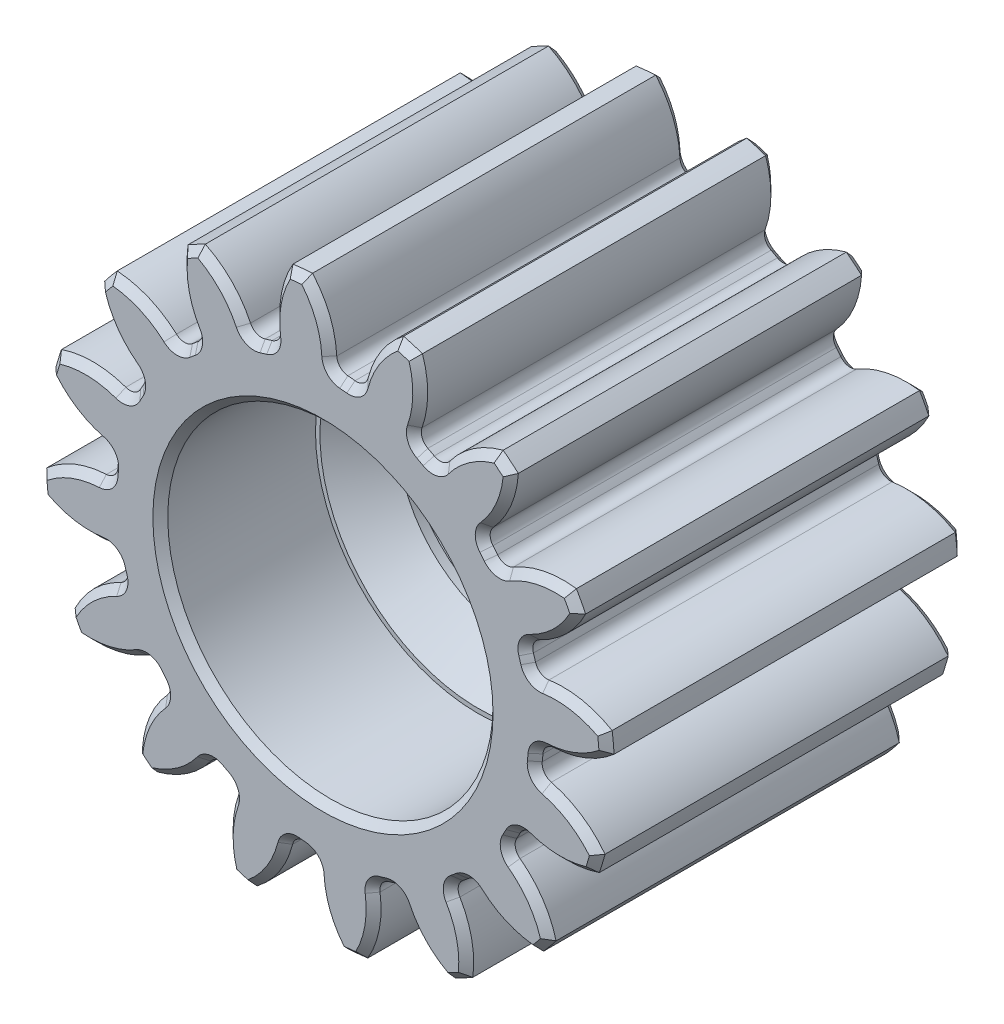
SolidWorks part; units mm, degrees
ref_plane "Front" through (0, 0, 0) normal (0, 0, 1) x (1, 0, 0)
ref_plane "Top" through (0, 0, 0) normal (0, 1, 0) x (1, 0, 0)
ref_plane "Right" through (0, 0, 0) normal (1, 0, 0) x (0, 0, -1)
sketch "Sketch3" plane through (0, 0, 0) normal (0, 0, 1) x (1, 0, 0)
  circle A0 centre (0, 0) radius 9.525
  dimension "od" = 19.05
extrude "gearBody" add sketch "Sketch3" along normal blind 12
sketch "Sketch2" plane through (0, 0, 0) normal (0, 0, 1) x (1, 0, 0)
  line L0 (0, 0) -> (7.3504, 3.0447) construction
  line L1 (9.6113, -3.1572) -> (0, 0) construction
  line L2 (0, 0) -> (36.3143, 0) construction
  line L3 (8.4666, -0.0191) -> (8.3054, -1.6447) construction
  line L5 (8.386, -0.8319) -> (0, 0) construction
  line L7 (0, 0) -> (7.9561, 0) construction
  arc A0 (7.9545, -0.1597) -> (7.8308, -1.4063) centre (0, 0) ccw construction
  arc A1 (9.5062, 0.5982) -> (9.2034, -2.4542) centre (0, 0) ccw construction
  arc A2 (8.4666, -0.0191) -> (8.3054, -1.6447) centre (0, 0) ccw construction
  arc A3 (7.098, -0.8257) -> (7.1219, -0.585) centre (0, 0) ccw
  arc A4 (9.6113, -3.1572) -> (7.4028, -1.2668) centre (6.609, -4.4295) ccw
  arc A5 (9.6113, -3.1572) -> (10.0443, 1.2073) centre (0, 0) ccw
  arc A6 (10.0443, 1.2073) -> (7.5074, -0.2123) centre (7.3504, 3.0447) cw
  arc A7 (7.1219, -0.585) -> (7.5074, -0.2123) centre (7.5269, -0.6183) cw
  arc A8 (7.4028, -1.2668) -> (7.098, -0.8257) centre (7.5017, -0.8726) cw
  point P6 (10.0443, 1.2073)
  point P22 (9.6113, -3.1572)
  dimension "baseDia" = 15.9121
  dimension "od" = 19.05
  dimension "pd" = 16.9333
  dimension "rd" = 14.2917
  dimension "rFillet" = 0.4064
  dimension "pointX" = 10.0443
  dimension "pointY" = 1.2073
  dimension "CTT" = 1.6256
  dimension "flankCenterAngle" = 22.5
extrude "toothCut" cut sketch "Sketch2" along normal through all
pattern_circular "CirPattern1" count 16 over 360 about axis through (0, 0, 0) along (0, 0, 1) of "toothCut"
sketch "hub1Dia" plane through (0, 0, 0) normal (0, 0, -1) x (-1, 0, 0)
  circle A0 centre (0, 0) radius 12.7
  dimension "hub1Dia" = 25.4
sketch "hub2Dia" plane through (0, 0, 12) normal (0, 0, 1) x (1, 0, 0)
  circle A0 centre (0, 0) radius 12.7
  dimension "hub2dia" = 25.4
sketch "boreDia" plane through (0, 0, 0) normal (0, 0, 1) x (1, 0, 0)
  circle A0 centre (0, 0) radius 4
  dimension "boreDia" = 8
extrude "bore" cut sketch "boreDia" against normal mid plane 25400
sketch "Sketch5" plane through (0, 0, 0) normal (0, 0, -1) x (-1, 0, 0)
  circle A0 centre (0, 0) radius 5.45
  dimension "D1" = 10.9
extrude "Cut-Extrude2" cut sketch "Sketch5" against normal blind 5.2
sketch "Sketch6" plane through (0, 0, 12) normal (0, 0, 1) x (1, 0, 0)
  circle A0 centre (0, 0) radius 5.45
  dimension "D1" = 10.9
extrude "Cut-Extrude3" cut sketch "Sketch6" against normal blind 5.2
sketch "Sketch7" plane through (0, 0, 12) normal (0, 0, 1) x (1, 0, 0)
  circle A96 centre (0, 0) radius 6.178
  arc A192 (7.1876, -6.4015) -> (7.6725, -5.8115) centre (0, 0) ccw
  arc A193 (7.6725, -5.8115) -> (6.4141, -3.923) centre (4.4108, -6.6214) ccw
  arc A194 (6.3291, -3.5278) -> (6.4141, -3.923) centre (6.5967, -3.677) ccw
  arc A195 (6.3291, -3.5278) -> (6.4448, -3.3116) centre (0, 0) ccw
  arc A196 (6.8209, -3.1632) -> (6.4448, -3.3116) centre (6.7174, -3.4516) ccw
  arc A197 (6.8209, -3.1632) -> (9.0902, -3.1636) centre (7.9561, 0) ccw
  arc A198 (9.0902, -3.1636) -> (9.3124, -2.4329) centre (0, 0) ccw
  arc A199 (9.3124, -2.4329) -> (7.4271, -1.1698) centre (6.609, -4.4295) ccw
  arc A200 (7.1973, -0.8372) -> (7.4271, -1.1698) centre (7.5017, -0.8726) ccw
  arc A201 (7.1973, -0.8372) -> (7.2215, -0.5932) centre (0, 0) ccw
  arc A202 (7.5122, -0.3122) -> (7.2215, -0.5932) centre (7.5269, -0.6183) ccw
  arc A203 (7.5122, -0.3122) -> (9.6089, 0.5559) centre (7.3504, 3.0447) ccw
  arc A204 (9.6089, 0.5559) -> (9.5346, 1.316) centre (0, 0) ccw
  arc A205 (9.5346, 1.316) -> (7.3094, 1.7615) centre (7.801, -1.5631) ccw
  arc A206 (6.9699, 1.9808) -> (7.3094, 1.7615) centre (7.2646, 2.0646) ccw
  arc A207 (6.9699, 1.9808) -> (6.8988, 2.2155) centre (0, 0) ccw
  arc A208 (7.0598, 2.5863) -> (6.8988, 2.2155) centre (7.1906, 2.3092) ccw
  arc A209 (7.0598, 2.5863) -> (8.6648, 4.1908) centre (5.6258, 5.6258) ccw
  arc A210 (8.6648, 4.1908) -> (8.3052, 4.8645) centre (0, 0) ccw
  arc A211 (8.3052, 4.8645) -> (6.0789, 4.4246) centre (7.8054, 1.5412) ccw
  arc A212 (5.6813, 4.4973) -> (6.0789, 4.4246) centre (5.9215, 4.6875) ccw
  arc A213 (5.6813, 4.4973) -> (5.5258, 4.687) centre (0, 0) ccw
  arc A214 (5.5327, 5.0911) -> (5.5258, 4.687) centre (5.7595, 4.8852) ccw
  arc A215 (5.5327, 5.0911) -> (6.4015, 7.1876) centre (3.0447, 7.3504) ccw
  arc A216 (6.4015, 7.1876) -> (5.8115, 7.6725) centre (0, 0) ccw
  arc A217 (5.8115, 7.6725) -> (3.923, 6.4141) centre (6.6214, 4.4108) ccw
  arc A218 (3.5278, 6.3291) -> (3.923, 6.4141) centre (3.677, 6.5967) ccw
  arc A219 (3.5278, 6.3291) -> (3.3116, 6.4448) centre (0, 0) ccw
  arc A220 (3.1632, 6.8209) -> (3.3116, 6.4448) centre (3.4516, 6.7174) ccw
  arc A221 (3.1632, 6.8209) -> (3.1636, 9.0902) centre (0, 7.9561) ccw
  arc A222 (3.1636, 9.0902) -> (2.4329, 9.3124) centre (0, 0) ccw
  arc A223 (2.4329, 9.3124) -> (1.1698, 7.4271) centre (4.4295, 6.609) ccw
  arc A224 (0.8372, 7.1973) -> (1.1698, 7.4271) centre (0.8726, 7.5017) ccw
  arc A225 (0.8372, 7.1973) -> (0.5932, 7.2215) centre (0, 0) ccw
  arc A226 (0.3122, 7.5122) -> (0.5932, 7.2215) centre (0.6183, 7.5269) ccw
  arc A227 (0.3122, 7.5122) -> (-0.5559, 9.6089) centre (-3.0447, 7.3504) ccw
  arc A228 (-0.5559, 9.6089) -> (-1.316, 9.5346) centre (0, 0) ccw
  arc A229 (-1.316, 9.5346) -> (-1.7615, 7.3094) centre (1.5631, 7.801) ccw
  arc A230 (-1.9808, 6.9699) -> (-1.7615, 7.3094) centre (-2.0646, 7.2646) ccw
  arc A231 (-1.9808, 6.9699) -> (-2.2155, 6.8988) centre (0, 0) ccw
  arc A232 (-2.5863, 7.0598) -> (-2.2155, 6.8988) centre (-2.3092, 7.1906) ccw
  arc A233 (-2.5863, 7.0598) -> (-4.1908, 8.6648) centre (-5.6258, 5.6258) ccw
  arc A234 (-4.1908, 8.6648) -> (-4.8645, 8.3052) centre (0, 0) ccw
  arc A235 (-4.8645, 8.3052) -> (-4.4246, 6.0789) centre (-1.5412, 7.8054) ccw
  arc A236 (-4.4973, 5.6813) -> (-4.4246, 6.0789) centre (-4.6875, 5.9215) ccw
  arc A237 (-4.4973, 5.6813) -> (-4.687, 5.5258) centre (0, 0) ccw
  arc A238 (-5.0911, 5.5327) -> (-4.687, 5.5258) centre (-4.8852, 5.7595) ccw
  arc A239 (-5.0911, 5.5327) -> (-7.1876, 6.4015) centre (-7.3504, 3.0447) ccw
  arc A240 (-7.1876, 6.4015) -> (-7.6725, 5.8115) centre (0, 0) ccw
  arc A241 (-7.6725, 5.8115) -> (-6.4141, 3.923) centre (-4.4108, 6.6214) ccw
  arc A242 (-6.3291, 3.5278) -> (-6.4141, 3.923) centre (-6.5967, 3.677) ccw
  arc A243 (-6.3291, 3.5278) -> (-6.4448, 3.3116) centre (0, 0) ccw
  arc A244 (-6.8209, 3.1632) -> (-6.4448, 3.3116) centre (-6.7174, 3.4516) ccw
  arc A245 (-6.8209, 3.1632) -> (-9.0902, 3.1636) centre (-7.9561, 0) ccw
  arc A246 (-9.0902, 3.1636) -> (-9.3124, 2.4329) centre (0, 0) ccw
  arc A247 (-9.3124, 2.4329) -> (-7.4271, 1.1698) centre (-6.609, 4.4295) ccw
  arc A248 (-7.1973, 0.8372) -> (-7.4271, 1.1698) centre (-7.5017, 0.8726) ccw
  arc A249 (-7.1973, 0.8372) -> (-7.2215, 0.5932) centre (0, 0) ccw
  arc A250 (-7.5122, 0.3122) -> (-7.2215, 0.5932) centre (-7.5269, 0.6183) ccw
  arc A251 (-7.5122, 0.3122) -> (-9.6089, -0.5559) centre (-7.3504, -3.0447) ccw
  arc A252 (-9.6089, -0.5559) -> (-9.5346, -1.316) centre (0, 0) ccw
  arc A253 (-9.5346, -1.316) -> (-7.3094, -1.7615) centre (-7.801, 1.5631) ccw
  arc A254 (-6.9699, -1.9808) -> (-7.3094, -1.7615) centre (-7.2646, -2.0646) ccw
  arc A255 (-6.9699, -1.9808) -> (-6.8988, -2.2155) centre (0, 0) ccw
  arc A256 (-7.0598, -2.5863) -> (-6.8988, -2.2155) centre (-7.1906, -2.3092) ccw
  arc A257 (-7.0598, -2.5863) -> (-8.6648, -4.1908) centre (-5.6258, -5.6258) ccw
  arc A258 (-8.6648, -4.1908) -> (-8.3052, -4.8645) centre (0, 0) ccw
  arc A259 (-8.3052, -4.8645) -> (-6.0789, -4.4246) centre (-7.8054, -1.5412) ccw
  arc A260 (-5.6813, -4.4973) -> (-6.0789, -4.4246) centre (-5.9215, -4.6875) ccw
  arc A261 (-5.6813, -4.4973) -> (-5.5258, -4.687) centre (0, 0) ccw
  arc A262 (-5.5327, -5.0911) -> (-5.5258, -4.687) centre (-5.7595, -4.8852) ccw
  arc A263 (-5.5327, -5.0911) -> (-6.4015, -7.1876) centre (-3.0447, -7.3504) ccw
  arc A264 (-6.4015, -7.1876) -> (-5.8115, -7.6725) centre (0, 0) ccw
  arc A265 (-5.8115, -7.6725) -> (-3.923, -6.4141) centre (-6.6214, -4.4108) ccw
  arc A266 (-3.5278, -6.3291) -> (-3.923, -6.4141) centre (-3.677, -6.5967) ccw
  arc A267 (-3.5278, -6.3291) -> (-3.3116, -6.4448) centre (0, 0) ccw
  arc A268 (-3.1632, -6.8209) -> (-3.3116, -6.4448) centre (-3.4516, -6.7174) ccw
  arc A269 (-3.1632, -6.8209) -> (-3.1636, -9.0902) centre (0, -7.9561) ccw
  arc A270 (-3.1636, -9.0902) -> (-2.4329, -9.3124) centre (0, 0) ccw
  arc A271 (-2.4329, -9.3124) -> (-1.1698, -7.4271) centre (-4.4295, -6.609) ccw
  arc A272 (-0.8372, -7.1973) -> (-1.1698, -7.4271) centre (-0.8726, -7.5017) ccw
  arc A273 (-0.8372, -7.1973) -> (-0.5932, -7.2215) centre (0, 0) ccw
  arc A274 (-0.3122, -7.5122) -> (-0.5932, -7.2215) centre (-0.6183, -7.5269) ccw
  arc A275 (-0.3122, -7.5122) -> (0.5559, -9.6089) centre (3.0447, -7.3504) ccw
  arc A276 (0.5559, -9.6089) -> (1.316, -9.5346) centre (0, 0) ccw
  arc A277 (1.316, -9.5346) -> (1.7615, -7.3094) centre (-1.5631, -7.801) ccw
  arc A278 (1.9808, -6.9699) -> (1.7615, -7.3094) centre (2.0646, -7.2646) ccw
  arc A279 (1.9808, -6.9699) -> (2.2155, -6.8988) centre (0, 0) ccw
  arc A280 (2.5863, -7.0598) -> (2.2155, -6.8988) centre (2.3092, -7.1906) ccw
  arc A281 (2.5863, -7.0598) -> (4.1908, -8.6648) centre (5.6258, -5.6258) ccw
  arc A282 (4.1908, -8.6648) -> (4.8645, -8.3052) centre (0, 0) ccw
  arc A283 (4.8645, -8.3052) -> (4.4246, -6.0789) centre (1.5412, -7.8054) ccw
  arc A284 (4.4973, -5.6813) -> (4.4246, -6.0789) centre (4.6875, -5.9215) ccw
  arc A285 (4.4973, -5.6813) -> (4.687, -5.5258) centre (0, 0) ccw
  arc A286 (5.0911, -5.5327) -> (4.687, -5.5258) centre (4.8852, -5.7595) ccw
  arc A287 (5.0911, -5.5327) -> (7.1876, -6.4015) centre (7.3504, -3.0447) ccw
  arc A288 (7.1876, -6.4015) -> (7.6725, -5.8115) centre (0, 0) ccw
  arc A289 (7.6725, -5.8115) -> (6.4141, -3.923) centre (4.4108, -6.6214) ccw
  arc A290 (6.3291, -3.5278) -> (6.4141, -3.923) centre (6.5967, -3.677) ccw
  arc A291 (6.3291, -3.5278) -> (6.4448, -3.3116) centre (0, 0) ccw
  arc A292 (6.8209, -3.1632) -> (6.4448, -3.3116) centre (6.7174, -3.4516) ccw
  arc A293 (6.8209, -3.1632) -> (9.0902, -3.1636) centre (7.9561, 0) ccw
  arc A294 (9.0902, -3.1636) -> (9.3124, -2.4329) centre (0, 0) ccw
  arc A295 (9.3124, -2.4329) -> (7.4271, -1.1698) centre (6.609, -4.4295) ccw
  arc A296 (7.1973, -0.8372) -> (7.4271, -1.1698) centre (7.5017, -0.8726) ccw
  arc A297 (7.1973, -0.8372) -> (7.2215, -0.5932) centre (0, 0) ccw
  arc A298 (7.5122, -0.3122) -> (7.2215, -0.5932) centre (7.5269, -0.6183) ccw
  arc A299 (7.5122, -0.3122) -> (9.6089, 0.5559) centre (7.3504, 3.0447) ccw
  arc A300 (9.6089, 0.5559) -> (9.5346, 1.316) centre (0, 0) ccw
  arc A301 (9.5346, 1.316) -> (7.3094, 1.7615) centre (7.801, -1.5631) ccw
  arc A302 (6.9699, 1.9808) -> (7.3094, 1.7615) centre (7.2646, 2.0646) ccw
  arc A303 (6.9699, 1.9808) -> (6.8988, 2.2155) centre (0, 0) ccw
  arc A304 (7.0598, 2.5863) -> (6.8988, 2.2155) centre (7.1906, 2.3092) ccw
  arc A305 (7.0598, 2.5863) -> (8.6648, 4.1908) centre (5.6258, 5.6258) ccw
  arc A306 (8.6648, 4.1908) -> (8.3052, 4.8645) centre (0, 0) ccw
  arc A307 (8.3052, 4.8645) -> (6.0789, 4.4246) centre (7.8054, 1.5412) ccw
  arc A308 (5.6813, 4.4973) -> (6.0789, 4.4246) centre (5.9215, 4.6875) ccw
  arc A309 (5.6813, 4.4973) -> (5.5258, 4.687) centre (0, 0) ccw
  arc A310 (5.5327, 5.0911) -> (5.5258, 4.687) centre (5.7595, 4.8852) ccw
  arc A311 (5.5327, 5.0911) -> (6.4015, 7.1876) centre (3.0447, 7.3504) ccw
  arc A312 (6.4015, 7.1876) -> (5.8115, 7.6725) centre (0, 0) ccw
  arc A313 (5.8115, 7.6725) -> (3.923, 6.4141) centre (6.6214, 4.4108) ccw
  arc A314 (3.5278, 6.3291) -> (3.923, 6.4141) centre (3.677, 6.5967) ccw
  arc A315 (3.5278, 6.3291) -> (3.3116, 6.4448) centre (0, 0) ccw
  arc A316 (3.1632, 6.8209) -> (3.3116, 6.4448) centre (3.4516, 6.7174) ccw
  arc A317 (3.1632, 6.8209) -> (3.1636, 9.0902) centre (0, 7.9561) ccw
  arc A318 (3.1636, 9.0902) -> (2.4329, 9.3124) centre (0, 0) ccw
  arc A319 (2.4329, 9.3124) -> (1.1698, 7.4271) centre (4.4295, 6.609) ccw
  arc A320 (0.8372, 7.1973) -> (1.1698, 7.4271) centre (0.8726, 7.5017) ccw
  arc A321 (0.8372, 7.1973) -> (0.5932, 7.2215) centre (0, 0) ccw
  arc A322 (0.3122, 7.5122) -> (0.5932, 7.2215) centre (0.6183, 7.5269) ccw
  arc A323 (0.3122, 7.5122) -> (-0.5559, 9.6089) centre (-3.0447, 7.3504) ccw
  arc A324 (-0.5559, 9.6089) -> (-1.316, 9.5346) centre (0, 0) ccw
  arc A325 (-1.316, 9.5346) -> (-1.7615, 7.3094) centre (1.5631, 7.801) ccw
  arc A326 (-1.9808, 6.9699) -> (-1.7615, 7.3094) centre (-2.0646, 7.2646) ccw
  arc A327 (-1.9808, 6.9699) -> (-2.2155, 6.8988) centre (0, 0) ccw
  arc A328 (-2.5863, 7.0598) -> (-2.2155, 6.8988) centre (-2.3092, 7.1906) ccw
  arc A329 (-2.5863, 7.0598) -> (-4.1908, 8.6648) centre (-5.6258, 5.6258) ccw
  arc A330 (-4.1908, 8.6648) -> (-4.8645, 8.3052) centre (0, 0) ccw
  arc A331 (-4.8645, 8.3052) -> (-4.4246, 6.0789) centre (-1.5412, 7.8054) ccw
  arc A332 (-4.4973, 5.6813) -> (-4.4246, 6.0789) centre (-4.6875, 5.9215) ccw
  arc A333 (-4.4973, 5.6813) -> (-4.687, 5.5258) centre (0, 0) ccw
  arc A334 (-5.0911, 5.5327) -> (-4.687, 5.5258) centre (-4.8852, 5.7595) ccw
  arc A335 (-5.0911, 5.5327) -> (-7.1876, 6.4015) centre (-7.3504, 3.0447) ccw
  arc A336 (-7.1876, 6.4015) -> (-7.6725, 5.8115) centre (0, 0) ccw
  arc A337 (-7.6725, 5.8115) -> (-6.4141, 3.923) centre (-4.4108, 6.6214) ccw
  arc A338 (-6.3291, 3.5278) -> (-6.4141, 3.923) centre (-6.5967, 3.677) ccw
  arc A339 (-6.3291, 3.5278) -> (-6.4448, 3.3116) centre (0, 0) ccw
  arc A340 (-6.8209, 3.1632) -> (-6.4448, 3.3116) centre (-6.7174, 3.4516) ccw
  arc A341 (-6.8209, 3.1632) -> (-9.0902, 3.1636) centre (-7.9561, 0) ccw
  arc A342 (-9.0902, 3.1636) -> (-9.3124, 2.4329) centre (0, 0) ccw
  arc A343 (-9.3124, 2.4329) -> (-7.4271, 1.1698) centre (-6.609, 4.4295) ccw
  arc A344 (-7.1973, 0.8372) -> (-7.4271, 1.1698) centre (-7.5017, 0.8726) ccw
  arc A345 (-7.1973, 0.8372) -> (-7.2215, 0.5932) centre (0, 0) ccw
  arc A346 (-7.5122, 0.3122) -> (-7.2215, 0.5932) centre (-7.5269, 0.6183) ccw
  arc A347 (-7.5122, 0.3122) -> (-9.6089, -0.5559) centre (-7.3504, -3.0447) ccw
  arc A348 (-9.6089, -0.5559) -> (-9.5346, -1.316) centre (0, 0) ccw
  arc A349 (-9.5346, -1.316) -> (-7.3094, -1.7615) centre (-7.801, 1.5631) ccw
  arc A350 (-6.9699, -1.9808) -> (-7.3094, -1.7615) centre (-7.2646, -2.0646) ccw
  arc A351 (-6.9699, -1.9808) -> (-6.8988, -2.2155) centre (0, 0) ccw
  arc A352 (-7.0598, -2.5863) -> (-6.8988, -2.2155) centre (-7.1906, -2.3092) ccw
  arc A353 (-7.0598, -2.5863) -> (-8.6648, -4.1908) centre (-5.6258, -5.6258) ccw
  arc A354 (-8.6648, -4.1908) -> (-8.3052, -4.8645) centre (0, 0) ccw
  arc A355 (-8.3052, -4.8645) -> (-6.0789, -4.4246) centre (-7.8054, -1.5412) ccw
  arc A356 (-5.6813, -4.4973) -> (-6.0789, -4.4246) centre (-5.9215, -4.6875) ccw
  arc A357 (-5.6813, -4.4973) -> (-5.5258, -4.687) centre (0, 0) ccw
  arc A358 (-5.5327, -5.0911) -> (-5.5258, -4.687) centre (-5.7595, -4.8852) ccw
  arc A359 (-5.5327, -5.0911) -> (-6.4015, -7.1876) centre (-3.0447, -7.3504) ccw
  arc A360 (-6.4015, -7.1876) -> (-5.8115, -7.6725) centre (0, 0) ccw
  arc A361 (-5.8115, -7.6725) -> (-3.923, -6.4141) centre (-6.6214, -4.4108) ccw
  arc A362 (-3.5278, -6.3291) -> (-3.923, -6.4141) centre (-3.677, -6.5967) ccw
  arc A363 (-3.5278, -6.3291) -> (-3.3116, -6.4448) centre (0, 0) ccw
  arc A364 (-3.1632, -6.8209) -> (-3.3116, -6.4448) centre (-3.4516, -6.7174) ccw
  arc A365 (-3.1632, -6.8209) -> (-3.1636, -9.0902) centre (0, -7.9561) ccw
  arc A366 (-3.1636, -9.0902) -> (-2.4329, -9.3124) centre (0, 0) ccw
  arc A367 (-2.4329, -9.3124) -> (-1.1698, -7.4271) centre (-4.4295, -6.609) ccw
  arc A368 (-0.8372, -7.1973) -> (-1.1698, -7.4271) centre (-0.8726, -7.5017) ccw
  arc A369 (-0.8372, -7.1973) -> (-0.5932, -7.2215) centre (0, 0) ccw
  arc A370 (-0.3122, -7.5122) -> (-0.5932, -7.2215) centre (-0.6183, -7.5269) ccw
  arc A371 (-0.3122, -7.5122) -> (0.5559, -9.6089) centre (3.0447, -7.3504) ccw
  arc A372 (0.5559, -9.6089) -> (1.316, -9.5346) centre (0, 0) ccw
  arc A373 (1.316, -9.5346) -> (1.7615, -7.3094) centre (-1.5631, -7.801) ccw
  arc A374 (1.9808, -6.9699) -> (1.7615, -7.3094) centre (2.0646, -7.2646) ccw
  arc A375 (1.9808, -6.9699) -> (2.2155, -6.8988) centre (0, 0) ccw
  arc A376 (2.5863, -7.0598) -> (2.2155, -6.8988) centre (2.3092, -7.1906) ccw
  arc A377 (2.5863, -7.0598) -> (4.1908, -8.6648) centre (5.6258, -5.6258) ccw
  arc A378 (4.1908, -8.6648) -> (4.8645, -8.3052) centre (0, 0) ccw
  arc A379 (4.8645, -8.3052) -> (4.4246, -6.0789) centre (1.5412, -7.8054) ccw
  arc A380 (4.4973, -5.6813) -> (4.4246, -6.0789) centre (4.6875, -5.9215) ccw
  arc A381 (4.4973, -5.6813) -> (4.687, -5.5258) centre (0, 0) ccw
  arc A382 (5.0911, -5.5327) -> (4.687, -5.5258) centre (4.8852, -5.7595) ccw
  arc A383 (5.0911, -5.5327) -> (7.1876, -6.4015) centre (7.3504, -3.0447) ccw
  dimension "D1" = 0.1
extrude "Boss-Extrude1" [suppressed] add sketch "Sketch7" against normal through all
chamfer "Chamfer1" distance 0.25 angle 45 194 edges at (6.0801, -6.0478, 12) (4.892, -5.3532, 12) (4.5294, -5.527, 12) (4.2877, -5.8484, 12) (4.7354, -7.1498, 12) (4.4841, -8.4035, 12) (3.3029, -7.9142, 12) (2.4711, -6.8178, 12) (2.0695, -6.8396, 12) (1.7232, -7.0441, 12) (1.6388, -8.4177, 12) (0.9269, -9.4798, 12) (0.0229, -8.5757, 12) (-0.3261, -7.2444, 12) (-0.7054, -7.111, 12) (-1.1036, -7.1673, 12) (-1.7073, -8.4041, 12) (-2.7714, -9.1129, 12) (-3.2607, -7.9317, 12) (-3.0736, -6.5682, 12) (-3.373, -6.2997, 12) (-3.7624, -6.1994, 12) (-4.7934, -7.111, 12) (-6.0478, -7.3587, 12) (-6.0478, -6.0801, 12) (-5.3532, -4.892, 12) (-5.527, -4.5294, 12) (-5.8484, -4.2877, 12) (-7.1498, -4.7354, 12) (-8.4035, -4.4841, 12) (-7.9142, -3.3029, 12) (-6.8178, -2.4711, 12) (-6.8396, -2.0695, 12) (-7.0441, -1.7232, 12) (-8.4177, -1.6388, 12) (-9.4798, -0.9269, 12) (-8.5757, -0.0229, 12) (-7.2444, 0.3261, 12) (-7.111, 0.7054, 12) (-7.1673, 1.1036, 12) (-8.4041, 1.7073, 12) (-9.1129, 2.7714, 12) (-7.9317, 3.2607, 12) (-6.5682, 3.0736, 12) (-6.2997, 3.373, 12) (-6.1994, 3.7624, 12) (-7.111, 4.7934, 12) (-7.3587, 6.0478, 12) (-6.0801, 6.0478, 12) (-4.892, 5.3532, 12) (-4.5294, 5.527, 12) (-4.2877, 5.8484, 12) (-4.7354, 7.1498, 12) (-4.4841, 8.4035, 12) (-3.3029, 7.9142, 12) (-2.4711, 6.8178, 12) (-2.0695, 6.8396, 12) (-1.7232, 7.0441, 12) (-1.6388, 8.4177, 12) (-0.9269, 9.4798, 12) (-0.0229, 8.5757, 12) (0.3261, 7.2444, 12) (0.7054, 7.111, 12) (1.1036, 7.1673, 12) (1.7073, 8.4041, 12) (2.7714, 9.1129, 12) (3.2607, 7.9317, 12) (3.0736, 6.5682, 12) (3.373, 6.2997, 12) (3.7624, 6.1994, 12) (4.7934, 7.111, 12) (6.0478, 7.3587, 12) (6.0478, 6.0801, 12) (5.3532, 4.892, 12) (5.527, 4.5294, 12) (5.8484, 4.2877, 12) (7.1498, 4.7354, 12) (8.4035, 4.4841, 12) (7.9142, 3.3029, 12) (6.8178, 2.4711, 12) (6.8396, 2.0695, 12) (7.0441, 1.7232, 12) (8.4177, 1.6388, 12) (9.4798, 0.9269, 12) (8.5757, 0.0229, 12) (7.2444, -0.3261, 12) (7.111, -0.7054, 12) (7.1673, -1.1036, 12) (8.4041, -1.7073, 12) (9.1129, -2.7714, 12) (7.9317, -3.2607, 12) (6.5682, -3.0736, 12) (6.2997, -3.373, 12) (6.1994, -3.7624, 12) (7.111, -4.7934, 12) (7.3587, -6.0478, 12) (5.45, 0, 12) (6.1994, -3.7624, 0) (6.2997, -3.373, 0) (6.5682, -3.0736, 0) (7.9317, -3.2607, 0) (9.1129, -2.7714, 0) (8.4041, -1.7073, 0) (7.1673, -1.1036, 0) (7.111, -0.7054, 0) (7.2444, -0.3261, 0) (8.5757, 0.0229, 0) (9.4798, 0.9269, 0) (8.4177, 1.6388, 0) (7.0441, 1.7232, 0) (6.8396, 2.0695, 0) (6.8178, 2.4711, 0) (7.9142, 3.3029, 0) (8.4035, 4.4841, 0) (7.1498, 4.7354, 0) (5.8484, 4.2877, 0) (5.527, 4.5294, 0) (5.3532, 4.892, 0) (6.0478, 6.0801, 0) (6.0478, 7.3587, 0) (4.7934, 7.111, 0) (3.7624, 6.1994, 0) (3.373, 6.2997, 0) (3.0736, 6.5682, 0) (3.2607, 7.9317, 0) (2.7714, 9.1129, 0) (1.7073, 8.4041, 0) (1.1036, 7.1673, 0) (0.7054, 7.111, 0) (0.3261, 7.2444, 0) (-0.0229, 8.5757, 0) (-0.9269, 9.4798, 0) (-1.6388, 8.4177, 0) (-1.7232, 7.0441, 0) (-2.0695, 6.8396, 0) (-2.4711, 6.8178, 0) (-3.3029, 7.9142, 0) (-4.4841, 8.4035, 0) (-4.7354, 7.1498, 0) (-4.2877, 5.8484, 0) (-4.5294, 5.527, 0) (-4.892, 5.3532, 0) (-6.0801, 6.0478, 0) (-7.3587, 6.0478, 0) (-7.111, 4.7934, 0) (-6.1994, 3.7624, 0) (-6.2997, 3.373, 0) (-6.5682, 3.0736, 0) (-7.9317, 3.2607, 0) (-9.1129, 2.7714, 0) (-8.4041, 1.7073, 0) (-7.1673, 1.1036, 0) (-7.111, 0.7054, 0) (-7.2444, 0.3261, 0) (-8.5757, -0.0229, 0) (-9.4798, -0.9269, 0) (-8.4177, -1.6388, 0) (-7.0441, -1.7232, 0) (-6.8396, -2.0695, 0) (-6.8178, -2.4711, 0) (-7.9142, -3.3029, 0) (-8.4035, -4.4841, 0) (-7.1498, -4.7354, 0) (-5.8484, -4.2877, 0) (-5.527, -4.5294, 0) (-5.3532, -4.892, 0) (-6.0478, -6.0801, 0) (-6.0478, -7.3587, 0) (-4.7934, -7.111, 0) (-3.7624, -6.1994, 0) (-3.373, -6.2997, 0) (-3.0736, -6.5682, 0) (-3.2607, -7.9317, 0) (-2.7714, -9.1129, 0) (-1.7073, -8.4041, 0) (-1.1036, -7.1673, 0) (-0.7054, -7.111, 0) (-0.3261, -7.2444, 0) (0.0229, -8.5757, 0) (0.9269, -9.4798, 0) (1.6388, -8.4177, 0) (1.7232, -7.0441, 0) (2.0695, -6.8396, 0) (2.4711, -6.8178, 0) (3.3029, -7.9142, 0) (4.4841, -8.4035, 0) (4.7354, -7.1498, 0) (4.2877, -5.8484, 0) (4.5294, -5.527, 0) (4.892, -5.3532, 0) (6.0801, -6.0478, 0) (7.3587, -6.0478, 0) (7.111, -4.7934, 0) (-5.45, 0, 0)
chamfer "Chamfer2" distance 1.3 angle 45 1 edges at (4, 0, 6.8)
